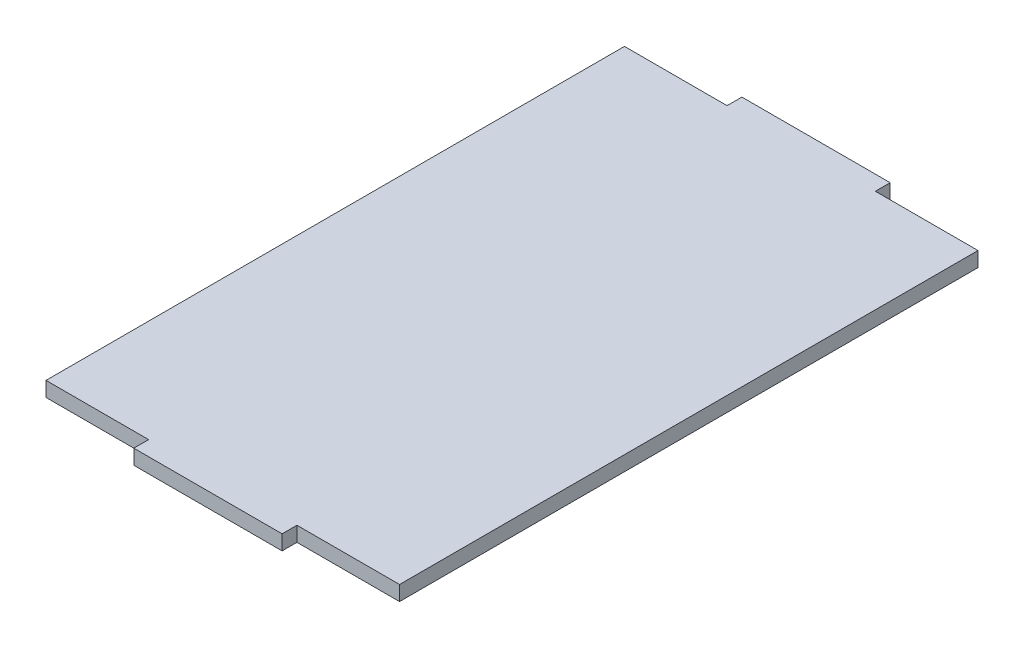
SolidWorks part; units mm, degrees
ref_plane "Front Plane" through (0, 0, 0) normal (0, 0, 1) x (1, 0, 0)
ref_plane "Top Plane" through (0, 0, 0) normal (0, 1, 0) x (1, 0, 0)
ref_plane "Right Plane" through (0, 0, 0) normal (1, 0, 0) x (0, 0, -1)
sketch "Sketch1" plane through (0, 0, 0) normal (0, 1, 0) x (1, 0, 0)
  line L0 (-17.4011, 29.1883) -> (12.5989, 29.1883)
  line L1 (-38.1561, 26.1883) -> (-17.4011, 26.1883)
  line L2 (-38.1561, 26.1883) -> (-38.1561, -90.8117)
  line L3 (-38.1561, -90.8117) -> (-17.4011, -90.8117)
  line L4 (33.3539, 26.1883) -> (33.3539, -90.8117)
  line L5 (-38.1561, 26.1883) -> (33.3539, -90.8117) construction
  line L6 (-38.1561, -90.8117) -> (33.3539, 26.1883) construction
  line L7 (-17.4011, -93.8117) -> (12.5989, -93.8117)
  line L8 (-2.4011, 29.1883) -> (-2.4011, 26.1883) construction
  line L9 (-2.4011, -90.8117) -> (-2.4011, -93.8117) construction
  line L10 (-17.4011, 29.1883) -> (-17.4011, 26.1883)
  line L11 (12.5989, 29.1883) -> (12.5989, 26.1883)
  line L12 (-17.4011, -90.8117) -> (-17.4011, -93.8117)
  line L13 (12.5989, -90.8117) -> (12.5989, -93.8117)
  line L14 (12.5989, 26.1883) -> (33.3539, 26.1883)
  line L15 (-38.1561, 29.1883) -> (33.3539, 29.1883) construction
  line L16 (12.5989, -90.8117) -> (33.3539, -90.8117)
  line L17 (-38.1561, 26.1883) -> (33.3539, 26.1883) construction
  line L18 (-38.1561, -93.8117) -> (33.3539, -93.8117) construction
  line L19 (-2.4011, 26.1883) -> (-2.4011, -32.3117) construction
  line L20 (-38.1561, -90.8117) -> (33.3539, -90.8117) construction
  line L21 (-2.4011, -90.8117) -> (-2.4011, -32.3117) construction
  point P4 (-2.4011, -32.3117)
  dimension "D1" = 71.51
  dimension "D2" = 117
  dimension "D3" = 3
  dimension "D4" = 3
  dimension "D5" = 15
  dimension "D6" = 15
  dimension "D7" = 15
  dimension "D8" = 15
extrude "Boss-Extrude1" add sketch "Sketch1" along normal blind 3
